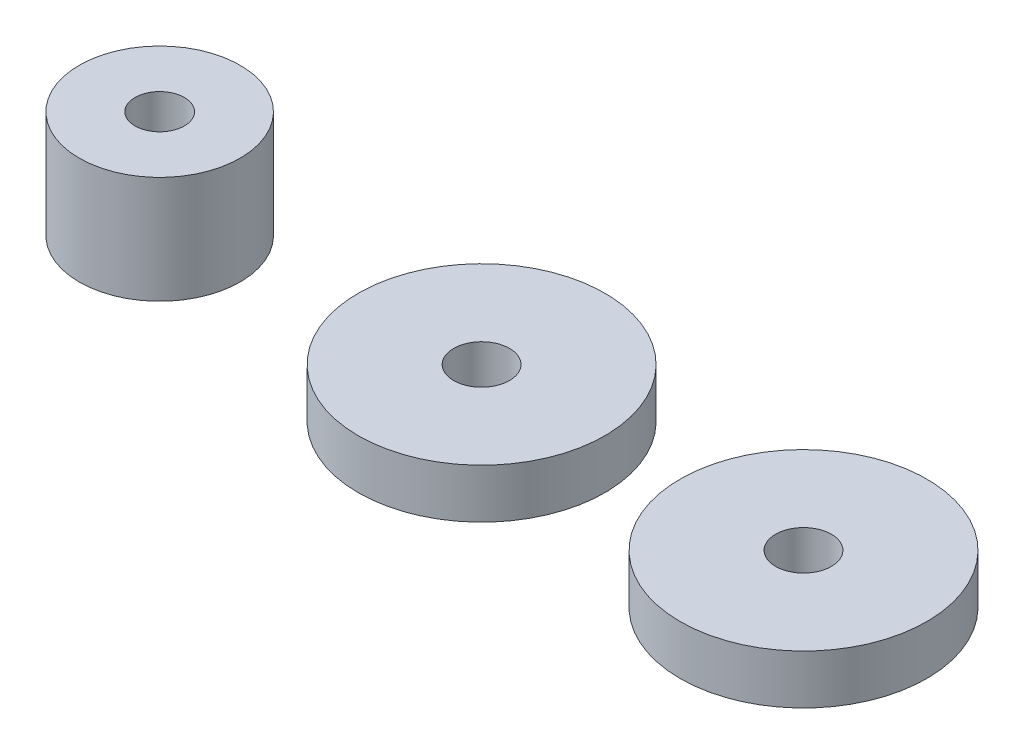
SolidWorks part; units mm, degrees
ref_plane "Front Plane" through (0, 0, 0) normal (0, 0, 1) x (1, 0, 0)
ref_plane "Top Plane" through (0, 0, 0) normal (0, 1, 0) x (1, 0, 0)
ref_plane "Right Plane" through (0, 0, 0) normal (1, 0, 0) x (0, 0, -1)
sketch "Sketch1" plane through (0, 0, 0) normal (0, 1, 0) x (1, 0, 0)
  circle A0 centre (0, 0) radius 1.15
  circle A1 centre (0, 0) radius 3.75
  dimension "D1" = 7.5
  dimension "D2" = 2.3
extrude "Boss-Extrude1" add sketch "Sketch1" along normal blind 5
sketch "Sketch2" plane through (0, 0, 0) normal (0, 1, 0) x (1, 0, 0)
  line L0 (0, 0) -> (15, 0) construction
  line L1 (15, 0) -> (30, 0) construction
  circle A0 centre (15, 0) radius 1.3
  circle A1 centre (15, 0) radius 5.75
  circle A2 centre (30, 0) radius 1.3
  circle A3 centre (30, 0) radius 5.75
  dimension "D1" = 11.5
  dimension "D3" = 2.6
  dimension "D4" = 11.5
  dimension "D6" = 2.6
  dimension "D2" = 15
  dimension "D5" = 15
extrude "Boss-Extrude2" add sketch "Sketch2" along normal blind 2.3 separate body
